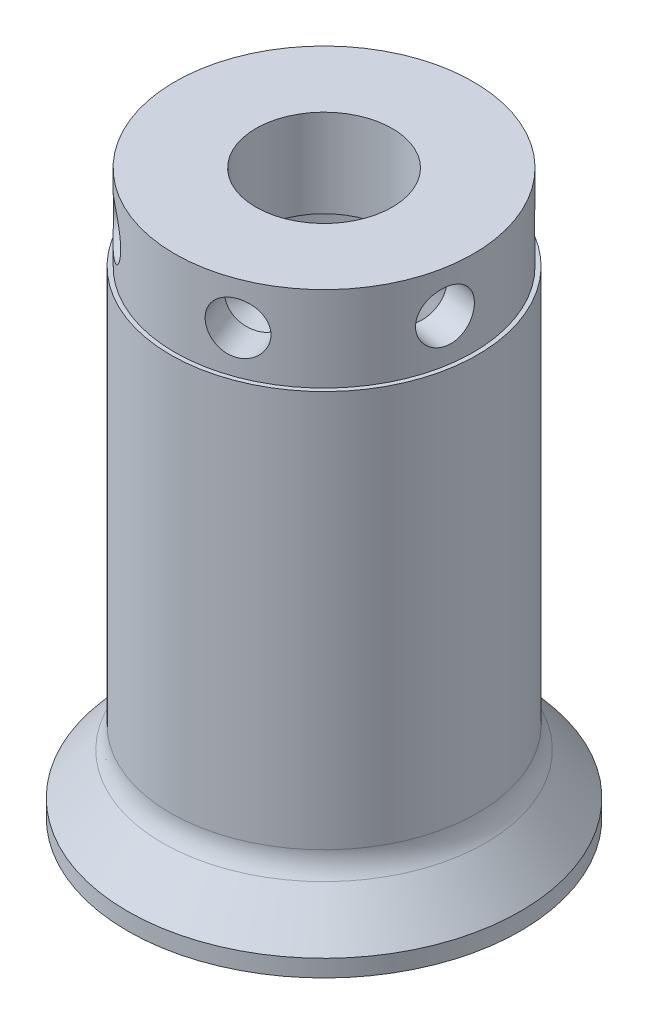
SolidWorks part; units mm, degrees
material "6061 Alloy"
ref_plane "Front" through (0, 0, 0) normal (0, 0, 1) x (1, 0, 0)
ref_plane "Top" through (0, 0, 0) normal (0, 1, 0) x (1, 0, 0)
ref_plane "Right" through (0, 0, 0) normal (1, 0, 0) x (0, 0, -1)
sketch "Sketch1" plane through (0, 0, 0) normal (1, 0, 0) x (0, 0, -1)
  line L0 (-18.288, 0) -> (-18.288, 1.5875)
  line L1 (-18.288, 1.5875) -> (-15.0314, 5.4644)
  line L2 (-14.2875, 7.5066) -> (-14.2875, 44.45)
  line L3 (-13.8906, 44.45) -> (-13.8906, 52.3875)
  line L4 (-13.8906, 52.3875) -> (0, 52.3875)
  line L5 (-13.8906, 44.45) -> (-14.2875, 44.45)
  line L6 (-18.288, 0) -> (0, 0)
  line L7 (0, 52.3875) -> (0, 0)
  arc A0 (-15.0314, 5.4644) -> (-14.2875, 7.5066) centre (-17.4625, 7.5066) ccw
  point P11 (-14.2875, 6.35)
  dimension "D8" = 3.175
  dimension "D1" = 18.288
  dimension "D2" = 1.5875
  dimension "D3" = 14.2875
  dimension "D4" = 44.45
  dimension "D5" = 0.3969
  dimension "D6" = 7.9375
  dimension "D7" = 4.7625
revolve "Revolve1" add sketch "Sketch1" angle 360 about L7
sketch "Sketch2" plane through (0, 0, 0) normal (0, -1, 0) x (1, 0, 0)
  circle A0 centre (0, 0) radius 13.8906
  circle A1 centre (0, 0) radius 13.8906 construction
extrude "Extrude2" cut sketch "Sketch2" against normal offset from surface (44.196 mm away) 0.254 up to face at (0, 44.45, 14.2875)
sketch "Sketch3" plane through (0, 0, 0) normal (0, 0, 1) x (1, 0, 0)
  line L0 (13.8906, 44.45) -> (13.8906, 52.3875) construction
  point P0 (13.8906, 48.4187)
hole_wizard "3/16 (0.1875) Diameter Hole1" positions "3DSketch1" profile "Sketch4" hole size "3/16" standard "Ansi Inch"
sketch3d "3DSketch1"
  point P0 (13.8906, 48.4187, 0)
  point P5 (13.7025, 48.4187, 2.2782)
  dimension "D1" = 3.9688
sketch "Sketch4" plane through (13.7025, 48.4187, 2.2782) normal (0, 1, 0) x (0.164, 0, -0.9865)
  line L0 (0, 0) -> (0, 4.7328)
  line L1 (0, 4.7328) -> (2.3812, 3.302)
  line L2 (2.3812, 3.302) -> (2.3812, 0)
  line L5 (2.3812, 0) -> (0, 0)
  line L10 (0, 4.7328) -> (-2.3813, 3.302) construction
  line L11 (0, -6.35) -> (0, 107.95) construction
  dimension "Hole Dia." = 4.7625
  dimension "Hole Depth" = 3.302
  dimension "Drill Angle" = 118
pattern_circular "CirPattern1" count 6 over 360 about axis through (0, 52.3875, 0) along (0, 1, 0) of "3/16 (0.1875) Diameter Hole1"
sketch "Sketch5" plane through (0, 52.3875, 0) normal (0, 1, 0) x (-1, 0, 0)
  circle A0 centre (0, 0) radius 6.35
  dimension "D1" = 12.7
extrude "Extrude3" cut sketch "Sketch5" against normal through all
